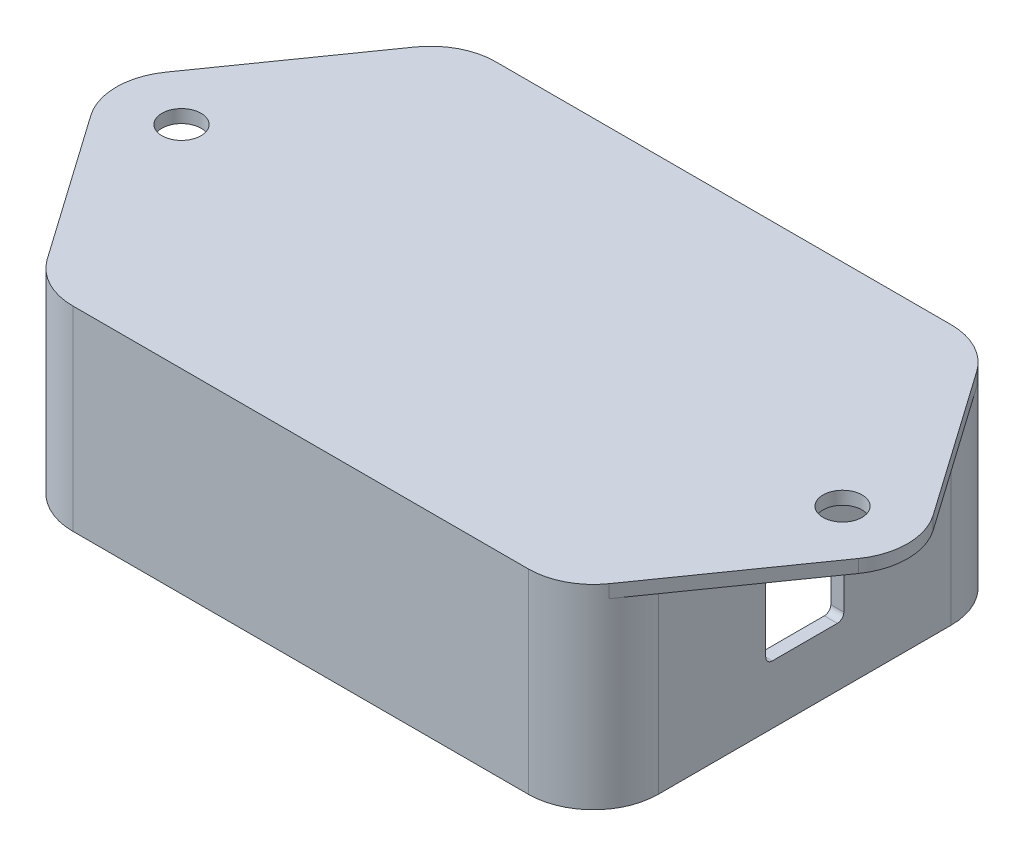
SolidWorks part; units mm, degrees
ref_plane "Plan de face" through (0, 0, 0) normal (0, 0, 1) x (1, 0, 0)
ref_plane "Plan de dessus" through (0, 0, 0) normal (0, 1, 0) x (1, 0, 0)
ref_plane "Plan de droite" through (0, 0, 0) normal (1, 0, 0) x (0, 0, -1)
ref_plane "Plan1" through (0, 7.6, 0) normal (0, -1, 0) x (1, 0, 0)
sketch "Esquisse1" plane through (0, 7.6, 0) normal (0, -1, 0) x (1, 0, 0)
  line L0 (63.0193, 0) -> (43.1838, 28.2468)
  line L1 (35, 32.5) -> (-35, 32.5)
  line L2 (-43.1838, 28.2468) -> (-63.0193, 0)
  line L3 (-63.0193, 0) -> (-43.1838, -28.2468)
  line L4 (-35, -32.5) -> (35, -32.5)
  line L5 (43.1838, -28.2468) -> (63.0193, 0)
  arc A0 (43.1838, 28.2468) -> (35, 32.5) centre (35, 22.5) ccw
  arc A1 (-35, 32.5) -> (-43.1838, 28.2468) centre (-35, 22.5) ccw
  arc A2 (-43.1838, -28.2468) -> (-35, -32.5) centre (-35, -22.5) ccw
  arc A3 (35, -32.5) -> (43.1838, -28.2468) centre (35, -22.5) ccw
extrude "Boss.-Extru.1" add sketch "Esquisse1" against normal blind 2
sketch "Esquisse2" plane through (0, 7.6, 0) normal (0, -1, 0) x (1, 0, 0)
  line L0 (-45, -22.5) -> (-45, 22.5)
  line L1 (-35, 32.5) -> (35, 32.5)
  line L2 (45, 22.5) -> (45, -22.5)
  line L3 (35, -32.5) -> (-35, -32.5)
  arc A0 (-45, 22.5) -> (-35, 32.5) centre (-35, 22.5) cw
  arc A1 (35, 32.5) -> (45, 22.5) centre (35, 22.5) cw
  arc A2 (45, -22.5) -> (35, -32.5) centre (35, -22.5) cw
  arc A3 (-35, -32.5) -> (-45, -22.5) centre (-35, -22.5) cw
extrude "Boss.-Extru.2" add sketch "Esquisse2" along normal blind 28
sketch "Esquisse3" plane through (0, -20.4, 0) normal (0, -1, 0) x (1, 0, 0)
  line L0 (43, -22.5) -> (43, 22.5)
  line L1 (35, 30.5) -> (-35, 30.5)
  line L2 (-43, 22.5) -> (-43, -22.5)
  line L3 (-35, -30.5) -> (35, -30.5)
  arc A0 (35, -30.5) -> (43, -22.5) centre (35, -22.5) ccw
  arc A1 (43, 22.5) -> (35, 30.5) centre (35, 22.5) ccw
  arc A2 (-35, 30.5) -> (-43, 22.5) centre (-35, 22.5) ccw
  arc A3 (-43, -22.5) -> (-35, -30.5) centre (-35, -22.5) ccw
extrude "Enlèv. mat.-Extru.1" cut sketch "Esquisse3" against normal blind 28
sketch "Esquisse4" plane through (0, 7.6, 0) normal (0, -1, 0) x (1, 0, 0)
  line L0 (42.7081, -15.5) -> (43, -15.5)
  line L1 (43, -15.5) -> (43, -18.5)
  line L2 (43, -18.5) -> (42.7081, -18.5)
  arc A0 (42.7081, -18.5) -> (42.7081, -15.5) centre (39, -17) cw
extrude "Boss.-Extru.3" add sketch "Esquisse4" along normal blind 22
sketch "Esquisse5" plane through (0, 7.6, 0) normal (0, -1, 0) x (1, 0, 0)
  line L0 (34.4928, -19.5157) -> (35.3469, -18.6294)
  line L1 (37.5072, -20.711) -> (36.6531, -21.5973)
  arc A0 (35.3469, -18.6294) -> (37.5072, -20.711) centre (39, -17) ccw
  arc A1 (36.6531, -21.5973) -> (34.4928, -19.5157) centre (33, -23.2267) cw
extrude "Boss.-Extru.4" add sketch "Esquisse5" along normal blind 6
sketch "Esquisse6" plane through (0, 7.6, 0) normal (0, -1, 0) x (1, 0, 0)
  line L0 (-42.7081, -18.5) -> (-43, -18.5)
  line L1 (-43, -18.5) -> (-43, -15.5)
  line L2 (-43, -15.5) -> (-42.7081, -15.5)
  arc A0 (-42.7081, -15.5) -> (-42.7081, -18.5) centre (-39, -17) cw
extrude "Boss.-Extru.5" add sketch "Esquisse6" along normal blind 22
sketch "Esquisse7" plane through (0, 7.6, 0) normal (0, -1, 0) x (1, 0, 0)
  line L0 (-36.6827, -21.4386) -> (-37.4386, -20.6827)
  line L1 (-35.3173, -18.5614) -> (-34.5614, -19.3173)
  arc A0 (-37.4386, -20.6827) -> (-35.3173, -18.5614) centre (-39, -17) ccw
  arc A1 (-34.5614, -19.3173) -> (-36.6827, -21.4386) centre (-33, -23) cw
extrude "Boss.-Extru.6" add sketch "Esquisse7" along normal blind 6
sketch "Esquisse8" plane through (0, 7.6, 0) normal (0, -1, 0) x (1, 0, 0)
  line L0 (42.7081, 18.5) -> (43, 18.5)
  line L1 (43, 18.5) -> (43, 15.5)
  line L2 (43, 15.5) -> (42.7081, 15.5)
  arc A0 (42.7081, 15.5) -> (42.7081, 18.5) centre (39, 17) cw
extrude "Boss.-Extru.7" add sketch "Esquisse8" along normal blind 22
sketch "Esquisse9" plane through (0, 7.6, 0) normal (0, -1, 0) x (1, 0, 0)
  line L0 (36.6827, 21.4386) -> (37.4386, 20.6827)
  line L1 (35.3173, 18.5614) -> (34.5614, 19.3173)
  arc A0 (37.4386, 20.6827) -> (35.3173, 18.5614) centre (39, 17) ccw
  arc A1 (34.5614, 19.3173) -> (36.6827, 21.4386) centre (33, 23) cw
extrude "Boss.-Extru.8" add sketch "Esquisse9" along normal blind 6
sketch "Esquisse10" plane through (0, 7.6, 0) normal (0, -1, 0) x (1, 0, 0)
  line L0 (-42.7081, 15.5) -> (-43, 15.5)
  line L1 (-43, 15.5) -> (-43, 18.5)
  line L2 (-43, 18.5) -> (-42.7081, 18.5)
  arc A0 (-42.7081, 18.5) -> (-42.7081, 15.5) centre (-39, 17) cw
extrude "Boss.-Extru.9" add sketch "Esquisse10" along normal blind 22
sketch "Esquisse11" plane through (0, 7.6, 0) normal (0, -1, 0) x (1, 0, 0)
  line L0 (-34.5614, 19.3173) -> (-35.3173, 18.5614)
  line L1 (-37.4386, 20.6827) -> (-36.6827, 21.4386)
  arc A0 (-35.3173, 18.5614) -> (-37.4386, 20.6827) centre (-39, 17) ccw
  arc A1 (-36.6827, 21.4386) -> (-34.5614, 19.3173) centre (-33, 23) cw
extrude "Boss.-Extru.10" add sketch "Esquisse11" along normal blind 6
sketch "Esquisse12" plane through (-45, 0, 0) normal (-1, 0, 0) x (0, 0, 1)
  line L0 (-6, -11.4) -> (6, -11.4)
  line L1 (6, -11.4) -> (6, 0.6)
  line L2 (6, 0.6) -> (-6, 0.6)
  line L3 (-6, 0.6) -> (-6, -11.4)
extrude "Enlèv. mat.-Extru.2" cut sketch "Esquisse12" against normal up to next
sketch "Esquisse13" plane through (45, 0, 0) normal (1, 0, 0) x (0, 0, -1)
  line L0 (6, 0.6) -> (-6, 0.6)
  line L1 (-6, 0.6) -> (-6, -11.4)
  line L2 (-6, -11.4) -> (6, -11.4)
  line L3 (6, -11.4) -> (6, 0.6)
extrude "Enlèv. mat.-Extru.3" cut sketch "Esquisse13" against normal through all
draft "Dépouille1" type of draft neutral plane draft angle 1 faces to draft 4 face at (-38.418, 0.6, 18.0091) face at (38.418, 0.6, 18.0091) face at (38.4368, 0.6, -18.0276) face at (-38.418, 0.6, -18.0091) neutral plane through (35, 7.6, -22.5) neutral plane normal (0, -1, 0) parameters "D1"=1
hole_wizard "Diamètre du perçage Ø6.0 (6)1" positions "Esquisse15" profile "Esquisse14" hole size "Ø6.0" standard "Ansi Metric"
sketch "Esquisse15" plane through (0, 9.6, 0) normal (0, 1, 0) x (1, 0, 0)
  point P0 (-50.8, 0)
  point P1 (50.8, 0)
sketch "Esquisse14" plane through (-50.8, 9.6, 0) normal (1, 0, 0) x (0, 0, 1)
  line L0 (0, 0) -> (0, 30)
  line L1 (0, 30) -> (3, 30)
  line L2 (3, 30) -> (3, 0)
  line L5 (3, 0) -> (0, 0)
  line L11 (0, -6.35) -> (0, 107.95) construction
  dimension "Diamètre du perçage jusqu'au prochain" = 6
  dimension "Profondeur du perçage jusqu'au prochain" = 30
hole_wizard "Diamètre du perçage Ø1.8 (1.8)1" positions "Esquisse17" profile "Esquisse16" hole size "Ø1.8" standard "Ansi Metric"
sketch "Esquisse17" plane through (0, 1.6, 0) normal (0, -1, 0) x (-1, 0, 0)
  point P0 (33, -23)
  point P1 (-33, -23)
  point P2 (-33, 23.2267)
  point P3 (33, 23)
sketch "Esquisse16" plane through (-33, 1.6, 23) normal (1, 0, 0) x (0, 0, -1)
  line L0 (0, 0) -> (0, 7)
  line L1 (0, 7) -> (0.9, 7)
  line L2 (0.9, 7) -> (0.9, 0)
  line L5 (0.9, 0) -> (0, 0)
  line L10 (0, 7) -> (-0.9, 7) construction
  line L11 (0, -6.35) -> (0, 107.95) construction
  dimension "Diamètre du perçage" = 1.8
  dimension "Profondeur du perçage" = 7
  dimension "Angle de pointe" = 180
hole_wizard "Perçage1" positions "Esquisse19" profile "Esquisse18" legacy
sketch "Esquisse19" plane through (0, -14.4, 0) normal (0, -1, 0) x (-1, 0, 0)
  point P0 (-39, 17)
  point P1 (-39, -17)
  point P2 (39, 17)
  point P3 (39, -17)
sketch "Esquisse18" plane through (39, -14.4, -17) normal (1, 0, 0) x (0, 0, -1)
  line L0 (0, 0) -> (0, 8)
  line L1 (0, 8) -> (1.325, 8)
  line L2 (1.325, 8) -> (1.325, 0)
  line L3 (1.325, 0) -> (0, 0)
  line L4 (0, 110) -> (0, -10) construction
  dimension "Diamètre" = 2.65
  dimension "Profondeur" = 8
fillet "Congé1" radius 1 8 edges at (-44, 0.6, -6) (44, 0.6, 6) (44, 0.6, -6) (-44, -11.4, 6) (-44, 0.6, 6) (44, -11.4, 6) (-44, -11.4, -6) (44, -11.4, -6)
fillet "Congé2" radius 10 2 edges at (63.0193, 8.6, 0) (-63.0193, 8.6, 0)
